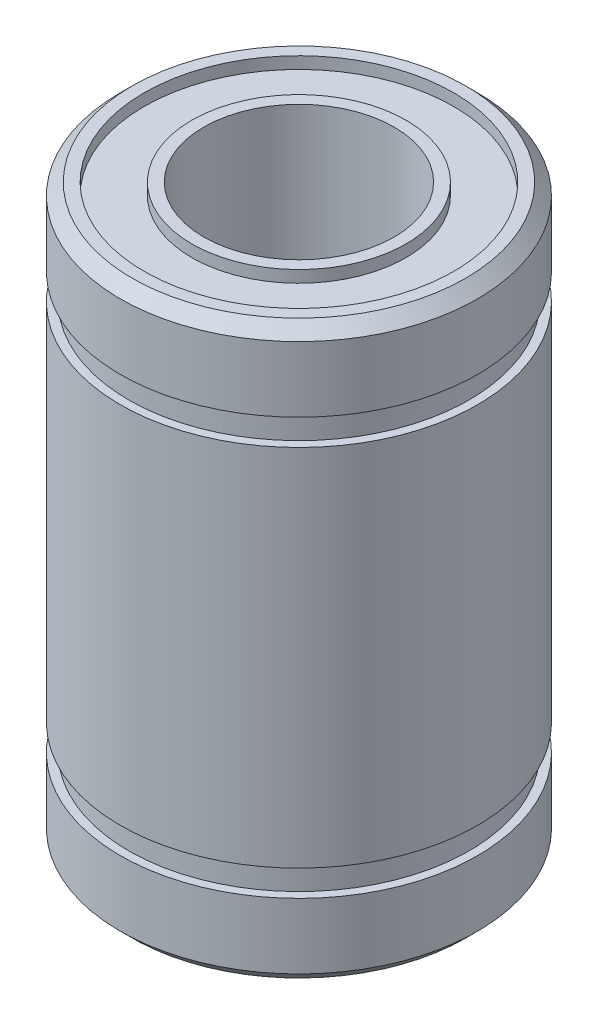
SolidWorks part; units mm, degrees
ref_plane "Front Plane" through (0, 0, 0) normal (0, 0, 1) x (1, 0, 0)
ref_plane "Top Plane" through (0, 0, 0) normal (0, 1, 0) x (1, 0, 0)
ref_plane "Right Plane" through (0, 0, 0) normal (1, 0, 0) x (0, 0, -1)
sketch "Sketch1" plane through (0, 0, 0) normal (0, 0, 1) x (1, 0, 0)
  line L0 (0, 12) -> (0, 0) construction
  line L1 (0, 0) -> (0, -12) construction
  line L2 (0, 12) -> (4, 12) construction
  line L3 (0, -12) -> (4, -12) construction
  line L4 (4, -12) -> (4, 12)
  line L5 (4, 12) -> (7, 12)
  line L6 (7, 12) -> (7.5, 11.5)
  line L7 (7.5, 11.5) -> (7.5, 8.75)
  line L8 (7.5, 7.65) -> (7.5, 8.75) construction
  line L9 (7.5, -8.75) -> (7.5, -7.65) construction
  line L10 (7.5, 7.65) -> (7.5, -7.65)
  line L11 (7.5, -11.5) -> (7, -11.5) construction
  line L12 (7, -11.5) -> (7, -12) construction
  line L13 (7.5, -8.75) -> (7.5, -11.5)
  line L14 (7.5, -11.5) -> (7, -12)
  line L15 (7, -12) -> (4, -12)
  line L16 (7.5, 11.5) -> (7, 11.5) construction
  line L17 (7, 11.5) -> (7, 12) construction
  line L18 (7, -11.5) -> (7, 11.5) construction
  line L19 (7.7571, -8.2) -> (7.7571, 8.2) construction
  line L20 (7.15, -8.2) -> (7.7571, -8.2) construction
  line L21 (7.5, 8.75) -> (7.15, 8.75)
  line L22 (0, 0) -> (7.5, 0) construction
  line L23 (7.15, 8.75) -> (7.15, 7.65)
  line L24 (7.15, 7.65) -> (7.5, 7.65)
  line L25 (7.5, -7.65) -> (7.15, -7.65)
  line L26 (7.15, -7.65) -> (7.15, -8.75)
  line L27 (7.15, -8.75) -> (7.5, -8.75)
  arc A0 (7.5, 8.75) -> (7.5, 7.65) centre (7.7571, 8.2) ccw construction
  arc A1 (7.5, -7.65) -> (7.5, -8.75) centre (7.7571, -8.2) ccw construction
  dimension "Total_length" = 24
  dimension "Inside_diameter" = 8
  dimension "D4" = 0.5
  dimension "Distance_between_lockingrings" = 17.5
  dimension "Diameter_outside" = 15
  dimension "Locking_ring_width" = 1.1
  dimension "Locking_ring_groove_dia" = 14.3
revolve "Body" add sketch "Sketch1" angle 360 about L0
sketch "Sketch2" plane through (0, 12, 0) normal (0, 1, 0) x (1, 0, 0)
  circle A0 centre (0, 0) radius 4.5
  circle A1 centre (0, 0) radius 6.5
  circle A2 centre (0, 0) radius 7.5 construction
  circle A3 centre (0, 0) radius 4 construction
  dimension "D1" = 1
  dimension "D2" = 0.5
extrude "Cut-Extrude1" cut sketch "Sketch2" against normal blind 0.5
mirror "Mirror1" about plane through (0, 0, 0) normal (0, 1, 0) of "Cut-Extrude1"
sketch "Sketch3" plane through (0, -11.5, 0) normal (0, -1, 0) x (1, 0, 0)
  line L0 (6.5, 0) -> (4.5, 0) construction
  circle A0 centre (0, 0) radius 5.1 construction
  circle A2 centre (0, 0) radius 6.5 construction
  circle A3 centre (0, 0) radius 4.5 construction
  text T0 "LM8UU" font "Century Gothic" height 0.8
  point P11 (5.5, 0)
  dimension "D1" = 0.4
split line "Split Line1"
